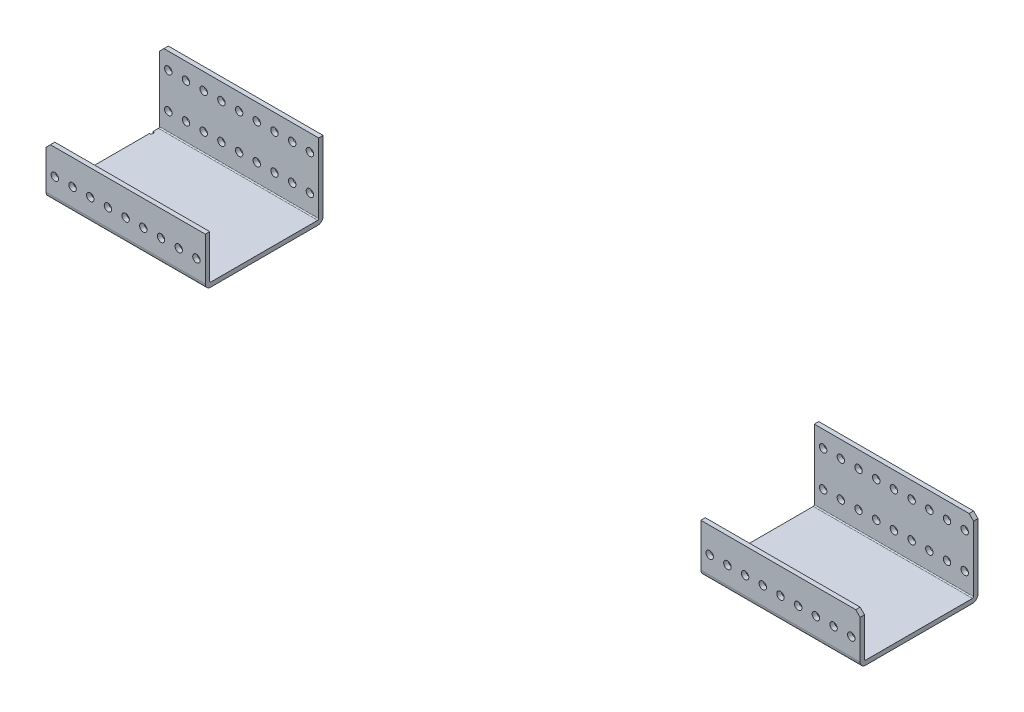
SolidWorks part; units mm, degrees
ref_plane "Front Plane" through (0, 0, 0) normal (0, 0, 1) x (1, 0, 0)
ref_plane "Top Plane" through (0, 0, 0) normal (0, 1, 0) x (1, 0, 0)
ref_plane "Right Plane" through (0, 0, 0) normal (1, 0, 0) x (0, 0, -1)
ref_plane "Plane1" through (0, 57.8164, 0) normal (0, 1, 0) x (1, 0, 0)
sketch "Sketch1" plane through (0, 57.8164, 0) normal (0, 1, 0) x (1, 0, 0)
  line L0 (488.098, -145.5605) -> (488.098, -60.9785)
  line L1 (488.098, -60.9785) -> (-96.102, -60.9785)
  line L2 (-96.102, -60.9785) -> (-96.102, -145.5605)
  line L3 (-96.102, -145.5605) -> (488.098, -145.5605)
extrude "Boss-Extrude1" add sketch "Sketch1" against normal blind 34.925
sketch "Sketch2" plane through (488.098, 0, 0) normal (1, 0, 0) x (0, 0, -1)
  line L0 (-60.9785, 57.8164) -> (-142.3855, 57.8164)
  line L1 (-142.3855, 57.8164) -> (-142.3855, 26.0664)
  line L2 (-142.3855, 26.0664) -> (-60.9785, 26.0664)
  line L3 (-60.9785, 26.0664) -> (-60.9785, 57.8164)
extrude "Cut-Extrude1" cut sketch "Sketch2" against normal through all
sketch "Sketch3" plane through (0, 26.0664, 0) normal (0, 1, 0) x (-1, 0, 0)
  line L0 (96.102, 60.9785) -> (-488.098, 60.9785)
  line L1 (-488.098, 60.9785) -> (-488.098, 64.1535)
  line L2 (-488.098, 64.1535) -> (96.102, 64.1535)
  line L3 (96.102, 64.1535) -> (96.102, 60.9785)
extrude "Boss-Extrude2" add sketch "Sketch3" along normal blind 50.8
hole_wizard "M2 Clearance Hole1" positions "Sketch5" profile "Sketch4" hole size "M2" standard "ANSI Metric"
sketch "Sketch5" plane through (0, 26.0664, 0) normal (0, 1, 0) x (1, 0, 0)
  point P0 (-96.102, -136.5435)
  point P1 (-96.102, -69.9955)
sketch "Sketch4" plane through (-96.102, 26.0664, 136.5435) normal (1, 0, 0) x (0, 0, 1)
  line L0 (0, 0) -> (0, 3.175)
  line L1 (0, 3.175) -> (1.27, 3.175)
  line L2 (1.27, 3.175) -> (1.27, 0)
  line L5 (1.27, 0) -> (0, 0)
  line L11 (0, -6.35) -> (0, 107.95) construction
  dimension "Thru Hole Dia." = 2.54
  dimension "Thru Hole Depth" = 3.175
hole_wizard "M5 Clearance Hole1" positions "Sketch7" profile "Sketch6" hole size "M5" standard "ANSI Metric"
sketch "Sketch7" plane through (0, 0, 60.9785) normal (0, 0, -1) x (-1, 0, 0)
  point P0 (-469.048, 64.9284)
  point P1 (-481.748, 64.9284)
  point P2 (-469.048, 39.5284)
  point P3 (-481.748, 39.5284)
  point P4 (-456.348, 39.5284)
  point P5 (-443.648, 39.5284)
  point P6 (-430.948, 39.5284)
  point P7 (-418.248, 39.5284)
  point P8 (-405.548, 39.5284)
  point P9 (-392.848, 39.5284)
  point P10 (-380.148, 39.5284)
  point P11 (-367.448, 39.5284)
  point P12 (-354.748, 39.5284)
  point P13 (-342.048, 39.5284)
  point P14 (-329.348, 39.5284)
  point P15 (-316.648, 39.5284)
  point P16 (-303.948, 39.5284)
  point P17 (-291.248, 39.5284)
  point P18 (-278.548, 39.5284)
  point P19 (-265.848, 39.5284)
  point P20 (-253.148, 39.5284)
  point P21 (-240.448, 39.5284)
  point P22 (-227.748, 39.5284)
  point P23 (-215.048, 39.5284)
  point P24 (-202.348, 39.5284)
  point P25 (-189.648, 39.5284)
  point P26 (-176.948, 39.5284)
  point P27 (-164.248, 39.5284)
  point P28 (-151.548, 39.5284)
  point P29 (-138.848, 39.5284)
  point P30 (-126.148, 39.5284)
  point P31 (-113.448, 39.5284)
  point P32 (-100.748, 39.5284)
  point P33 (-88.048, 39.5284)
  point P34 (-75.348, 39.5284)
  point P35 (-62.648, 39.5284)
  point P36 (-49.948, 39.5284)
  point P37 (-37.248, 39.5284)
  point P38 (-24.548, 39.5284)
  point P39 (-11.848, 39.5284)
  point P40 (0.852, 39.5284)
  point P41 (13.552, 39.5284)
  point P42 (26.252, 39.5284)
  point P43 (38.952, 39.5284)
  point P44 (51.652, 39.5284)
  point P45 (64.352, 39.5284)
  point P46 (77.052, 39.5284)
  point P47 (89.752, 39.5284)
  point P48 (-456.348, 64.9284)
  point P49 (-443.648, 64.9284)
  point P50 (-430.948, 64.9284)
  point P51 (-418.248, 64.9284)
  point P52 (-405.548, 64.9284)
  point P53 (-392.848, 64.9284)
  point P54 (-380.148, 64.9284)
  point P55 (-367.448, 64.9284)
  point P56 (-354.748, 64.9284)
  point P57 (-342.048, 64.9284)
  point P58 (-329.348, 64.9284)
  point P59 (-316.648, 64.9284)
  point P60 (-303.948, 64.9284)
  point P61 (-291.248, 64.9284)
  point P62 (-278.548, 64.9284)
  point P63 (-265.848, 64.9284)
  point P64 (-253.148, 64.9284)
  point P65 (-240.448, 64.9284)
  point P66 (-227.748, 64.9284)
  point P67 (-215.048, 64.9284)
  point P68 (-202.348, 64.9284)
  point P69 (-189.648, 64.9284)
  point P70 (-176.948, 64.9284)
  point P71 (-164.248, 64.9284)
  point P72 (-151.548, 64.9284)
  point P73 (-138.848, 64.9284)
  point P74 (-126.148, 64.9284)
  point P75 (-113.448, 64.9284)
  point P76 (-100.748, 64.9284)
  point P77 (-88.048, 64.9284)
  point P78 (-75.348, 64.9284)
  point P79 (-62.648, 64.9284)
  point P80 (-49.948, 64.9284)
  point P81 (-37.248, 64.9284)
  point P82 (-24.548, 64.9284)
  point P83 (-11.848, 64.9284)
  point P84 (0.852, 64.9284)
  point P85 (13.552, 64.9284)
  point P86 (26.252, 64.9284)
  point P87 (38.952, 64.9284)
  point P88 (51.652, 64.9284)
  point P89 (64.352, 64.9284)
  point P90 (77.052, 64.9284)
  point P91 (89.752, 64.9284)
sketch "Sketch6" plane through (469.048, 64.9284, 60.9785) normal (1, 0, 0) x (0, 1, 0)
  line L0 (0, 0) -> (0, 84.582)
  line L1 (0, 84.582) -> (2.667, 84.582)
  line L2 (2.667, 84.582) -> (2.667, 0)
  line L5 (2.667, 0) -> (0, 0)
  line L11 (0, -6.35) -> (0, 107.95) construction
  dimension "Thru Hole Dia." = 5.334
  dimension "Thru Hole Depth" = 84.582
chamfer "Chamfer1" distance 3.175 angle 45 4 edges at (488.098, 76.8664, 62.566) (-96.102, 57.8164, 143.973) (488.098, 57.8164, 143.973) (-96.102, 76.8664, 62.566)
fillet "Fillet1" radius 0.762 2 edges at (195.998, 26.0664, 64.1535) (195.998, 26.0664, 142.3855)
fillet "Fillet2" radius 3.937 2 edges at (195.998, 22.8914, 145.5605) (195.998, 22.8914, 60.9785)
sketch "Sketch9" plane through (0, 0, 60.9785) normal (0, 0, -1) x (-1, 0, 0)
  line L0 (-484.923, 76.8664) -> (92.927, 76.8664) construction
  line L1 (-18.198, 76.8664) -> (-373.798, 76.8664)
  line L2 (-18.198, 76.8664) -> (-18.198, -19.9384)
  line L3 (-18.198, -19.9384) -> (-373.798, -19.9384)
  line L4 (-373.798, 76.8664) -> (-373.798, -19.9384)
  line L5 (96.102, 26.8284) -> (96.102, 73.6914) construction
  line L6 (-488.098, 26.8284) -> (-488.098, 73.6914) construction
  line L7 (96.102, 50.2599) -> (-18.198, 50.2599) construction
  line L8 (-488.098, 50.2599) -> (-373.798, 50.2599) construction
  dimension "D1" = 114.3
extrude "Cut-Extrude2" cut sketch "Sketch9" against normal through all
